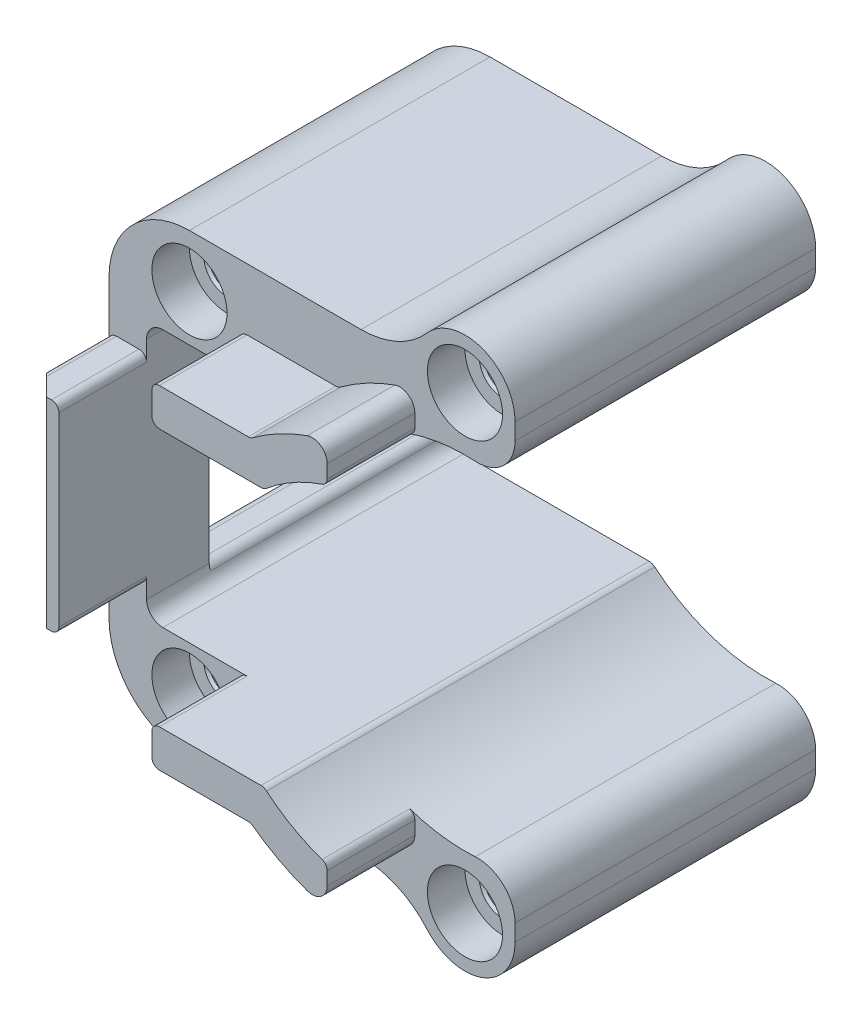
SolidWorks part; units mm, degrees
ref_plane "Front Plane" through (0, 0, 0) normal (0, 0, 1) x (1, 0, 0)
ref_plane "Top Plane" through (0, 0, 0) normal (0, 1, 0) x (1, 0, 0)
ref_plane "Right Plane" through (0, 0, 0) normal (1, 0, 0) x (0, 0, -1)
sketch "Sketch1" plane through (0, 0, 0) normal (0, 0, 1) x (1, 0, 0)
  line L12 (0, 18) -> (0, -18) construction
  line L13 (-22, -14) -> (-22, 14) construction
  line L14 (-9.293, 10.3) -> (-24.1216, 10.3)
  line L17 (-25.1216, 9) -> (-25.1216, -9) construction
  line L18 (-24.1216, -10) -> (-9.293, -10) construction
  line L19 (-9.293, 10) -> (-24.1216, 10) construction
  line L20 (-25.4216, 9) -> (-25.4216, -9)
  line L21 (-24.1216, -10.3) -> (-9.293, -10.3)
  line L22 (-28.4216, -9) -> (-28.4216, -11.8)
  line L23 (-22, -18.2216) -> (-8.2975, -18.2216)
  line L24 (27.9046, 0) -> (-28.4216, 0) construction
  line L25 (4, -18) -> (4, -13.1031)
  line L26 (-25.4216, -9) -> (-28.4216, -9)
  line L27 (4, 18) -> (4, 13.1031)
  line L28 (-22, 18.2216) -> (-8.2975, 18.2216)
  line L29 (-28.4216, 9) -> (-28.4216, 11.8)
  line L30 (-25.4216, 9) -> (-28.4216, 9)
  circle A2 centre (0, -18) radius 1.65
  circle A4 centre (0, 18) radius 1.65
  circle A5 centre (-22, 14) radius 1.65
  circle A6 centre (-22, -14) radius 1.65
  arc A7 (-24.1216, 10.3) -> (-25.4216, 9) centre (-24.1216, 9) ccw
  arc A8 (-25.4216, -9) -> (-24.1216, -10.3) centre (-24.1216, -9) ccw
  arc A9 (-8.8413, -10.4653) -> (-9.293, -10.3) centre (-9.293, -11) ccw
  arc A10 (-8.8413, -10.4653) -> (-8.8413, 10.4653) centre (0, 0) ccw
  arc A11 (-24.1216, 10) -> (-25.1216, 9) centre (-24.1216, 9) ccw construction
  arc A16 (-25.1216, -9) -> (-24.1216, -10) centre (-24.1216, -9) ccw construction
  arc A17 (-8.6477, -10.2361) -> (-9.293, -10) centre (-9.293, -11) ccw construction
  arc A18 (-8.6477, -10.2361) -> (-8.6477, 10.2361) centre (0, 0) ccw construction
  arc A19 (-9.293, 10) -> (-8.6477, 10.2361) centre (-9.293, 11) ccw construction
  arc A20 (-9.293, 10.3) -> (-8.8413, 10.4653) centre (-9.293, 11) ccw
  arc A21 (-28.4216, -11.8) -> (-22, -18.2216) centre (-22, -11.8) ccw
  arc A22 (-3.0173, -20.626) -> (-8.2975, -18.2216) centre (-8.2975, -25.2216) ccw
  arc A23 (-3.0173, -20.626) -> (4, -18) centre (0, -18) ccw
  arc A24 (-3.0173, 20.626) -> (4, 18) centre (0, 18) cw
  arc A25 (-3.0173, 20.626) -> (-8.2975, 18.2216) centre (-8.2975, 25.2216) cw
  arc A26 (-28.4216, 11.8) -> (-22, 18.2216) centre (-22, 11.8) cw
  point P1 (-25.1216, 0)
  point P11 (0, 0)
  point P17 (-22, 0)
  dimension "D1" = 20
  dimension "D3" = 13.4
  dimension "D4" = 1
  dimension "D5" = 36
  dimension "D6" = 3.3
  dimension "D12" = 4
  dimension "D13" = 7
  dimension "D2" = 25.1216
  dimension "D7" = 28
  dimension "D8" = 22
  dimension "D10" = 3
  dimension "D11" = 1.5
  dimension "D9" = 0.3
extrude "Boss-Extrude1" add sketch "Sketch1" along normal blind 24 contours A26 L29 L30 A7 L14 A20 A10 L27 A24 A25 L28 A5 A4 | A22 A23 L25 A10 A9 L21 A8 L26 L22 A21 L23 A2 A6
sketch "Sketch4" plane through (0, 0, 0) normal (0, 0, 1) x (1, 0, 0)
  circle A0 centre (0, 0) radius 12.3139
sketch "Sketch5" plane through (0, 0, 24) normal (0, 0, 1) x (1, 0, 0)
  circle A0 centre (-22, 14) radius 3
  circle A1 centre (0, 18) radius 3
  circle A2 centre (0, -18) radius 3
  circle A3 centre (-22, -14) radius 3
  dimension "D1" = 6
extrude "Cut-Extrude1" cut sketch "Sketch5" against normal blind 3
sketch "Sketch6" plane through (0, 0, 24) normal (0, 0, 1) x (1, 0, 0)
  line L1 (-28.4216, 9) -> (-25.4216, 9)
  line L2 (-28.4216, 9) -> (-28.4216, -9)
  line L3 (-28.4216, -9) -> (-25.4216, -9)
  line L4 (-25.4216, 9) -> (-25.4216, -9)
  line L5 (-28.4216, 9) -> (-25.4216, -9) construction
  line L6 (-28.4216, -9) -> (-25.4216, 9) construction
  point P4 (-26.9216, 0)
extrude "Boss-Extrude2" add sketch "Sketch6" against normal blind 5
fillet "Fillet1" radius 3 2 edges at (4, -13.1031, 12) (4, 13.1031, 12)
sketch "Sketch7" plane through (0, 0, 24) normal (0, 0, 1) x (1, 0, 0)
  line L0 (-25.4216, -9) -> (-25.4216, 9) construction
  line L1 (-28.4216, 8) -> (-25.4216, 8)
  line L2 (-28.4216, 8) -> (-28.4216, -8)
  line L3 (-28.4216, -8) -> (-25.4216, -8)
  line L4 (-25.4216, 8) -> (-25.4216, -8)
  line L5 (-28.4216, 8) -> (-25.4216, -8) construction
  line L6 (-28.4216, -8) -> (-25.4216, 8) construction
  line L7 (-18, 10.3) -> (-9.293, 10.3)
  line L8 (-9.293, 10.3) -> (-24.1216, 10.3) construction
  line L9 (-18, 10.3) -> (-18, 13.3)
  line L10 (-18, 13.3) -> (-10.0995, 13.3)
  line L11 (-4, 13.1031) -> (-4, 16.2139)
  line L12 (0, 0) -> (-3.2863, 13.3) construction
  line L13 (-3.2863, 13.3) -> (-4.006, 16.2124) construction
  line L14 (0, 0) -> (-18.7555, 0) construction
  line L15 (-18, -10.3) -> (-9.293, -10.3)
  line L16 (-18, -10.3) -> (-18, -13.3)
  line L17 (-18, -13.3) -> (-10.0995, -13.3)
  line L18 (-4, -13.1031) -> (-4, -16.2139)
  arc A0 (-9.293, 10.3) -> (-8.8413, 10.4653) centre (-9.293, 11) ccw construction
  arc A1 (-9.293, 10.3) -> (-8.8413, 10.4653) centre (-9.293, 11) ccw
  arc A2 (-8.8413, 10.4653) -> (-4, 13.1031) centre (0, 0) cw
  arc A3 (-10.0995, 13.3) -> (-4, 16.2139) centre (0, 0) cw
  arc A4 (0.8204, 13.6754) -> (-8.8413, 10.4653) centre (0, 0) ccw construction
  circle A5 centre (-22, 14) radius 1.65 construction
  circle A6 centre (0, 18) radius 1.65 construction
  arc A7 (-8.8413, -10.4653) -> (-4, -13.1031) centre (0, 0) ccw
  arc A8 (-9.293, -10.3) -> (-8.8413, -10.4653) centre (-9.293, -11) cw
  arc A9 (-10.0995, -13.3) -> (-4, -16.2139) centre (0, 0) ccw
  point P4 (-26.9216, 0)
  dimension "D1" = 4
  dimension "D2" = 4
  dimension "D3" = 3
  dimension "D4" = 16
extrude "Boss-Extrude3" add sketch "Sketch7" along normal blind 7
chamfer "Chamfer1" distance 2 angle 45 1 edges at (-28.4216, 0, 31)
fillet "Fillet2" radius 0.6 12 edges at (-10.0995, -13.3, 27.5) (-4, -13.1031, 27.5) (-28.4216, -8, 26.5) (-25.4216, -8, 27.5) (-18, -10.3, 27.5) (-18, -13.3, 27.5) (-25.4216, 8, 27.5) (-28.4216, 8, 26.5) (-4, 13.1031, 27.5) (-10.0995, 13.3, 27.5) (-18, 13.3, 27.5) (-18, 10.3, 27.5)
fillet "Fillet3" radius 1.2 2 edges at (-4, -16.2139, 27.5) (-4, 16.2139, 27.5)
chamfer "Chamfer2" distance 0.2 angle 45 4 edges at (-20.35, -14, 21) (1.65, -18, 21) (-20.35, 14, 21) (1.65, 18, 21)
fillet "Fillet4" radius 0.8 4 edges at (-28.4216, -9, 9.5) (-25.4216, -9, 9.5) (-25.4216, 9, 9.5) (-28.4216, 9, 9.5)
